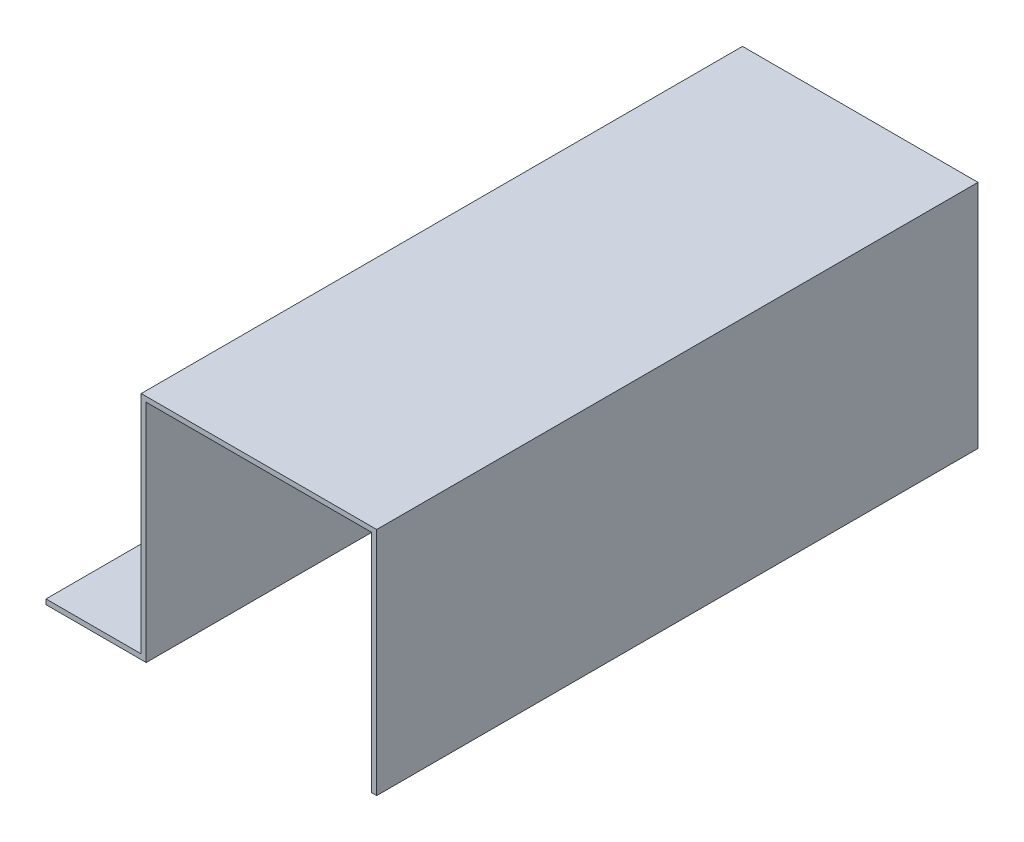
SolidWorks part; units mm, degrees
ref_plane "Front Plane" through (0, 0, 0) normal (0, 0, 1) x (1, 0, 0)
ref_plane "Top Plane" through (0, 0, 0) normal (0, 1, 0) x (1, 0, 0)
ref_plane "Right Plane" through (0, 0, 0) normal (1, 0, 0) x (0, 0, -1)
sketch "Sketch1" plane through (0, 0, 0) normal (0, 0, 1) x (1, 0, 0)
  line L0 (0, 0) -> (20, 0)
  line L1 (20, 0) -> (20, 45)
  line L2 (20, 45) -> (65, 45)
  line L3 (65, 45) -> (65, 0)
  line L4 (0, 0) -> (0, 1)
  line L5 (0, 1) -> (19, 1)
  line L6 (19, 1) -> (19, 46)
  line L7 (19, 46) -> (66, 46)
  line L8 (66, 46) -> (66, 0)
  line L9 (66, 0) -> (65, 0)
  point P11 (20, 22.5)
  dimension "D1" = 1
  dimension "D2" = 1
  dimension "D3" = 1
  dimension "D4" = 1
  dimension "D5" = 20
  dimension "D6" = 45
  dimension "D7" = 45
extrude "Boss-Extrude1" add sketch "Sketch1" along normal blind 120
sketch "Sketch2" plane through (0, 1, 0) normal (0, 1, 0) x (1, 0, 0)
  line L0 (9.5, 0) -> (9.5, -120) construction
  line L1 (19, 0) -> (0, 0) construction
  line L2 (19, -120) -> (0, -120) construction
  circle A0 centre (9.5, -30) radius 2.65
  circle A1 centre (9.5, -90) radius 2.65
  dimension "D1" = 5.3
  dimension "D2" = 5.3
  dimension "D4" = 30
  dimension "D3" = 30
extrude "Cut-Extrude1" cut sketch "Sketch2" against normal blind 200
